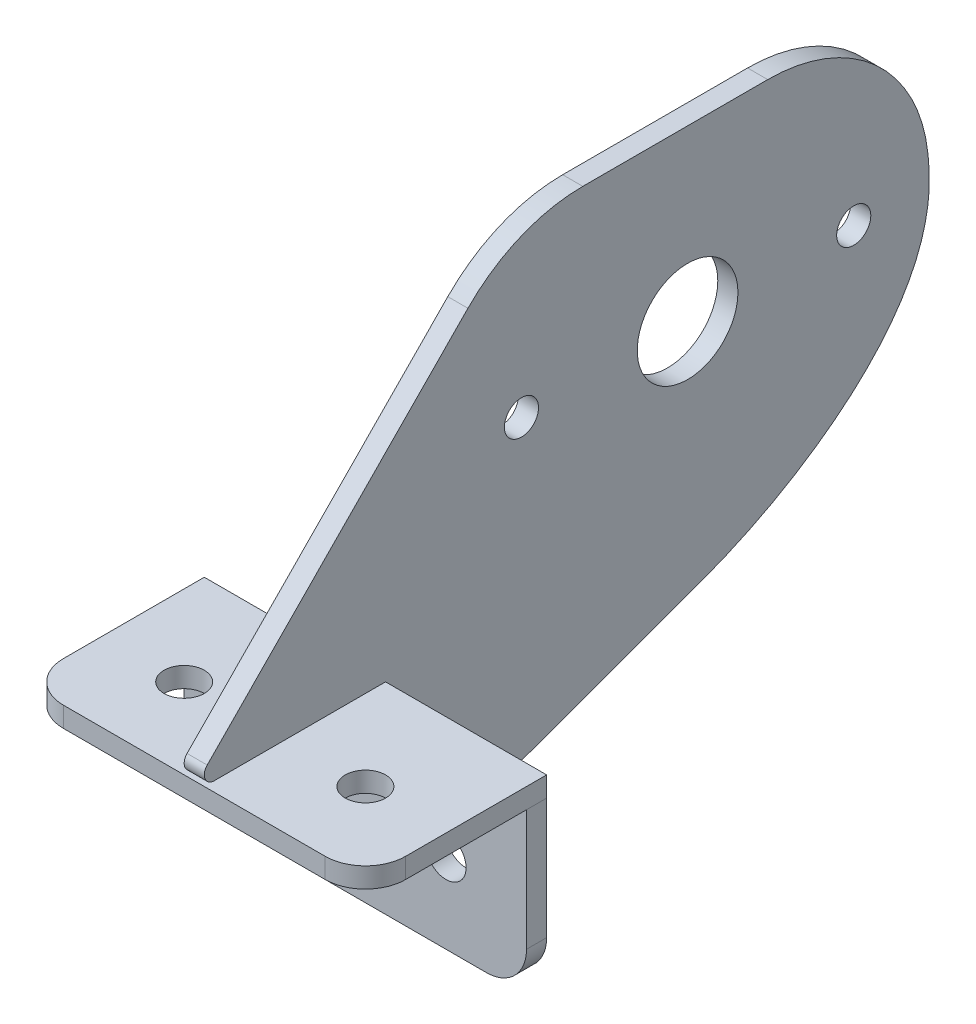
SolidWorks part; units mm, degrees
material "6061-T6 (SS)"
ref_plane "Front Plane" through (0, 0, 0) normal (0, 0, 1) x (1, 0, 0)
ref_plane "Top Plane" through (0, 0, 0) normal (0, 1, 0) x (1, 0, 0)
ref_plane "Right Plane" through (0, 0, 0) normal (1, 0, 0) x (0, 0, -1)
sketch "Sketch1" plane through (0, 0, 0) normal (1, 0, 0) x (0, 0, -1)
  line L0 (-27.1696, 26.71) -> (-75.7434, -22.6997)
  line L1 (-74.6113, -25.4001) -> (-47.6238, -25.4001)
  line L2 (-47.6238, -25.4001) -> (-47.6238, -52.3876)
  line L3 (-45.4933, -53.8794) -> (2.243, -36.5048)
  line L5 (-50.7988, -50.8255) -> (-50.7988, -47.6082) construction
  line L7 (-53.9484, -28.5751) -> (-57.1657, -28.5751) construction
  circle A0 centre (0, 0) radius 7.9375
  arc A1 (-27.1696, 26.71) -> (38.0986, 0.325) centre (0, 0) cw
  arc A2 (-75.7434, -22.6997) -> (-74.6113, -25.4001) centre (-74.6113, -23.8126) ccw
  arc A4 (-47.6238, -52.3876) -> (-45.4933, -53.8794) centre (-46.0363, -52.3876) ccw
  spline S0 degree 3 poles (38.0986, 0.325) (38.2579, -18.351) (16.1304, -31.4502) (2.243, -36.5048) knots 0 0 0 0 1 1 1 1
  point P15 (-76.1988, -23.8126)
  point P16 (-46.0363, -53.9751)
  point P22 (-50.7988, -49.2169)
  dimension "D1" = 15.875
  dimension "D2" = 1.5875
  dimension "D5" = 50.8
  dimension "D6" = 38.1
  dimension "D3" = 28.575
  dimension "D4" = 28.575
  dimension "D7" = 3.175
  dimension "D8" = 3.175
  dimension "D9" = 70
  dimension "D10" = 135
extrude "Boss-Extrude1" add sketch "Sketch1" along normal blind 3.175
sketch "Sketch2" plane through (38.0988, -25.4001, 0) normal (0, -1, 0) x (0, 0, -1)
  line L0 (-76.1988, -34.9238) -> (-76.1988, -38.0988) construction
  line L1 (-69.8488, -9.5238) -> (-47.6238, -9.5238)
  line L2 (-76.1988, -15.8738) -> (-76.1988, -57.1488)
  line L3 (-69.8488, -63.4988) -> (-47.6238, -63.4988)
  line L4 (-47.6238, -9.5238) -> (-47.6238, -63.4988)
  line L5 (-47.6238, -34.9238) -> (-47.6238, -38.0988) construction
  line L6 (-74.6113, -34.9238) -> (-47.6238, -34.9238) construction
  line L7 (-74.6113, -38.0988) -> (-47.6238, -38.0988) construction
  line L8 (-76.1988, -9.5238) -> (-50.7988, -34.9238) construction
  line L9 (-76.1988, -63.4988) -> (-50.7988, -38.0988) construction
  circle A1 centre (-63.4988, -22.2238) radius 3.175
  circle A2 centre (-63.4988, -50.7988) radius 3.175
  arc A3 (-76.1988, -57.1488) -> (-69.8488, -63.4988) centre (-69.8488, -57.1488) ccw
  arc A4 (-69.8488, -9.5238) -> (-76.1988, -15.8738) centre (-69.8488, -15.8738) ccw
  dimension "D3" = 6.35
  dimension "D4" = 6.35
  dimension "D1" = 25.4
  dimension "D2" = 25.4
  dimension "D5" = 3.175
extrude "Boss-Extrude2" add sketch "Sketch2" along normal blind 3.175 separate body
sketch "Sketch3" plane through (0, 0, 47.6238) normal (0, 0, 1) x (1, 0, 0)
  line L1 (-25.4, -28.5751) -> (28.575, -28.5751)
  line L2 (-25.4, -28.5751) -> (-25.4, -47.6251)
  line L3 (-19.05, -53.9751) -> (22.225, -53.9751)
  line L4 (28.575, -28.5751) -> (28.575, -47.6251)
  line L6 (-25.4, -28.5751) -> (0, -53.9751) construction
  line L7 (0, -52.3876) -> (0, -53.9751) construction
  line L8 (28.575, -28.5751) -> (3.175, -53.9751) construction
  line L9 (3.175, -25.4001) -> (3.175, -52.3876) construction
  circle A0 centre (-12.7, -41.2751) radius 3.175
  circle A1 centre (15.875, -41.2751) radius 3.175
  arc A2 (-25.4, -47.6251) -> (-19.05, -53.9751) centre (-19.05, -47.6251) ccw
  arc A3 (22.225, -53.9751) -> (28.575, -47.6251) centre (22.225, -47.6251) ccw
  dimension "D1" = 6.35
  dimension "D2" = 6.35
extrude "Boss-Extrude3" add sketch "Sketch3" along normal blind 3.175 separate body
sketch "Sketch4" plane through (3.175, 0, 0) normal (1, 0, 0) x (0, 0, -1)
  line L0 (-26.1937, 0) -> (26.1937, 0) construction
  line L1 (27.1696, 26.71) -> (-27.1696, 26.71)
  circle A0 centre (-26.1937, 0) radius 2.6924
  circle A1 centre (26.1937, 0) radius 2.6924
  arc A2 (38.0986, 0.325) -> (-27.1696, 26.71) centre (0, 0) ccw construction
  arc A3 (27.1696, 26.71) -> (-27.1696, 26.71) centre (0, 0) ccw
  point P4 (-27.5966, 26.2685)
  dimension "D1" = 5.3848
  dimension "D2" = 52.3875
extrude "Cut-Extrude1" cut sketch "Sketch4" against normal through all
fillet "Fillet1" radius 25.4 2 edges at (1.5875, 26.71, 27.1696) (1.5875, 26.71, -27.1696)
